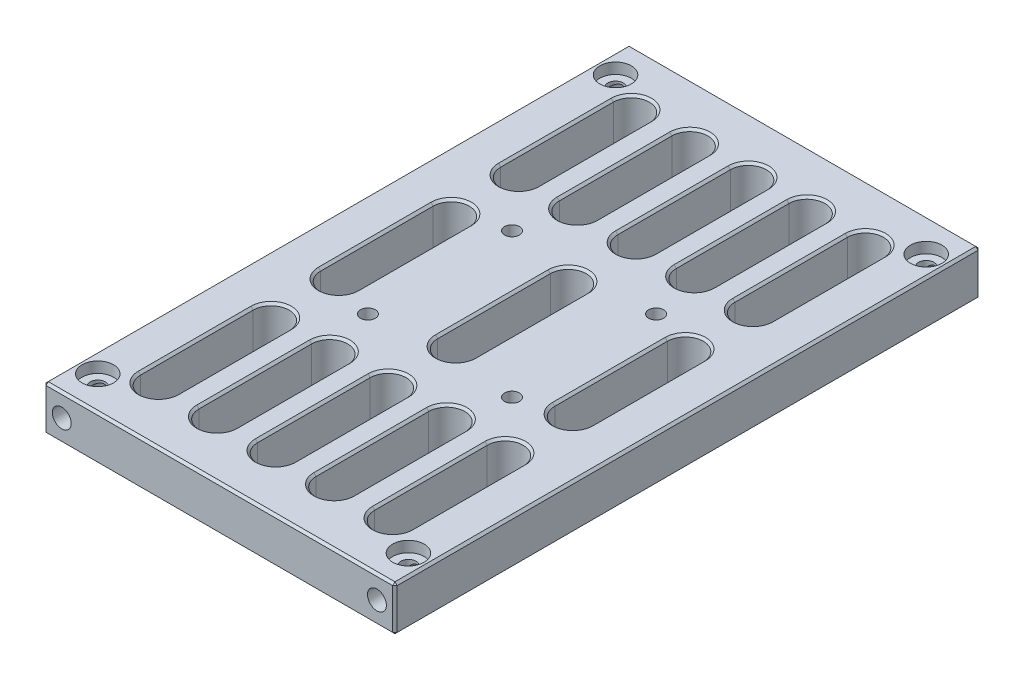
SolidWorks part; units mm, degrees
ref_plane "Plan de face" through (0, 0, 0) normal (0, 0, 1) x (1, 0, 0)
ref_plane "Plan de dessus" through (0, 0, 0) normal (0, 1, 0) x (1, 0, 0)
ref_plane "Plan de droite" through (0, 0, 0) normal (1, 0, 0) x (0, 0, -1)
sketch "Esquisse1" plane through (0, 0, 0) normal (0, 0, 1) x (1, 0, 0)
  line L1 (-39, 0.2172) -> (39, 0.2172)
  line L2 (-39, 0.2172) -> (-39, -9.7828)
  line L3 (-39, -9.7828) -> (39, -9.7828)
  line L4 (39, 0.2172) -> (39, -9.7828)
extrude "Boss.-Extru.1" add sketch "Esquisse1" along normal blind 130
sketch "Esquisse2" plane through (0, 0, 130) normal (0, 0, 1) x (1, 0, 0)
  line L0 (-52.4107, -4.7828) -> (51.3292, -4.7828) construction
  line L1 (39, 0.2172) -> (-39, 0.2172) construction
  line L2 (-35, 10.8156) -> (-35, -20.714) construction
  line L3 (35, 10.8156) -> (35, -20.714) construction
hole_wizard "Trou taraudé M5x0.81" positions "Esquisse3D1" profile "Esquisse3" tap size "M5x0.8" standard "Ansi Metric"
sketch3d "Esquisse3D1"
  line L0 (-52.4107, -4.7828, 130) -> (51.3292, -4.7828, 130) construction
  line L1 (-35, 10.8156, 130) -> (-35, -20.714, 130) construction
  line L2 (35, 10.8156, 130) -> (35, -20.714, 130) construction
  point P0 (-35, -4.7828, 130)
  point P6 (35, -4.7828, 130)
cosmetic thread "Filetage de perçage1" parameters "D1"=25, "D2"=5
cosmetic thread "Filetage de perçage2" parameters "D1"=25, "D2"=5
sketch "Esquisse3" plane through (-35, -4.7828, 130) normal (1, 0, 0) x (0, -1, 0)
  line L0 (0, 0) -> (0, 26.2618)
  line L1 (0, 26.2618) -> (2.1, 25)
  line L2 (2.1, 25) -> (2.1, 0)
  line L5 (2.1, 0) -> (0, 0)
  line L10 (0, 26.2618) -> (-2.1, 25) construction
  line L11 (0, -6.35) -> (0, 107.95) construction
  dimension "Diamètre du trou pour taraudage" = 4.2
  dimension "Profondeur du trou pour taraudage" = 25
  dimension "Angle de pointe" = 118
hole_wizard "Trou taraudé M5x0.82" positions "Esquisse4" profile "Esquisse5" tap size "M5x0.8" standard "Ansi Metric"
sketch "Esquisse4" plane through (0, 0, 0) normal (0, 0, -1) x (-1, 0, 0)
  line L0 (200052.4107, -4.7828) -> (-200051.3292, -4.7828) construction
  line L1 (-35, 10.8156) -> (-35, -20.714) construction
  line L2 (35, 10.8156) -> (35, -20.714) construction
  point P0 (-35, -4.7828)
  point P6 (35, -4.7828)
sketch "Esquisse5" plane through (35, -4.7828, 0) normal (1, 0, 0) x (0, 1, 0)
  line L0 (0, 0) -> (0, 29.4618)
  line L1 (0, 29.4618) -> (2.1, 28.2)
  line L2 (2.1, 28.2) -> (2.1, 0)
  line L5 (2.1, 0) -> (0, 0)
  line L10 (0, 29.4618) -> (-2.1, 28.2) construction
  line L11 (0, -6.35) -> (0, 107.95) construction
  dimension "Diamètre du trou pour taraudage" = 4.2
  dimension "Profondeur du trou pour taraudage" = 28.2
  dimension "Angle de pointe" = 118
cosmetic thread "Filetage de perçage3" parameters "D1"=24.2, "D2"=5
cosmetic thread "Filetage de perçage4" parameters "D1"=24.2, "D2"=5
sketch "Esquisse6" plane through (0, 0.2172, 0) normal (0, 1, 0) x (1, 0, 0)
  line L0 (0, 12.0068) -> (0, -135.3984) construction
  line L1 (54.4844, -65) -> (-55.2769, -65) construction
  line L2 (54.4844, -49) -> (-55.2769, -49) construction
  line L3 (16, -91.2165) -> (16, -33.1658) construction
  line L4 (54.4844, -81) -> (-55.2769, -81) construction
  line L5 (-16, -91.2165) -> (-16, -33.1658) construction
  dimension "D1" = 16
  dimension "D2" = 16
  dimension "D3" = 16
  dimension "D4" = 16
hole_wizard "Trou taraudé M4x0.71" positions "Esquisse3D2" profile "Esquisse7" tap size "M4x0.7" standard "Ansi Metric" end condition up to next
sketch3d "Esquisse3D2"
  line L0 (16, 0.2172, 91.2165) -> (16, 0.2172, 33.1658) construction
  line L1 (54.4844, 0.2172, 81) -> (-55.2769, 0.2172, 81) construction
  line L2 (54.4844, 0.2172, 49) -> (-55.2769, 0.2172, 49) construction
  line L3 (-16, 0.2172, 91.2165) -> (-16, 0.2172, 33.1658) construction
  point P0 (16, 0.2172, 81)
  point P6 (16, 0.2172, 49)
  point P10 (-16, 0.2172, 49)
  point P14 (-16, 0.2172, 81)
sketch "Esquisse7" plane through (16, 0.2172, 81) normal (1, 0, 0) x (0, 0, 1)
  line L0 (0, 0) -> (0, 10)
  line L1 (0, 10) -> (1.65, 10)
  line L2 (1.65, 10) -> (1.65, 0)
  line L5 (1.65, 0) -> (0, 0)
  line L11 (0, -6.35) -> (0, 107.95) construction
  dimension "Diamètre du trou pour taraudage jusqu'au prochain" = 3.3
  dimension "Profondeur du trou pour taraudage jusqu'au prochain" = 10
cosmetic thread "Filetage de perçage5" parameters "D2"=4
cosmetic thread "Filetage de perçage6" parameters "D2"=4
cosmetic thread "Filetage de perçage7" parameters "D2"=4
cosmetic thread "Filetage de perçage8" parameters "D2"=4
sketch "Esquisse8" plane through (0, 0.2172, 0) normal (0, 1, 0) x (1, 0, 0)
  line L0 (-34.5, 44.3525) -> (-34.5, -155.5225) construction
  line L1 (34.5, 44.3525) -> (34.5, -155.5225) construction
  line L2 (-62.6243, -7.5) -> (73.6594, -7.5) construction
  line L3 (39, 0) -> (-39, 0) construction
  line L4 (-62.6243, -122.5) -> (73.6594, -122.5) construction
  line L5 (39, -130) -> (-39, -130) construction
  dimension "D1" = 34.5
  dimension "D2" = 69
  dimension "D3" = 7.5
  dimension "D4" = 7.5
hole_wizard "Chambrage pour vis à tête ronde bombée M31" positions "Esquisse9" profile "Esquisse10" counterbore size "M3" standard "Ansi Metric" end condition through all
sketch "Esquisse9" plane through (0, 0.2172, 0) normal (0, 1, 0) x (1, 0, 0)
  line L0 (-34.5, 44.3525) -> (-34.5, -155.5225) construction
  line L1 (-62.6243, -7.5) -> (73.6594, -7.5) construction
  line L2 (34.5, 44.3525) -> (34.5, -155.5225) construction
  line L3 (-62.6243, -122.5) -> (73.6594, -122.5) construction
  point P0 (-34.5, -7.5)
  point P6 (34.5, -7.5)
  point P10 (34.5, -122.5)
  point P14 (-34.5, -122.5)
sketch "Esquisse10" plane through (-34.5, 0.2172, 7.5) normal (1, 0, 0) x (0, 0, 1)
  line L0 (0, 0) -> (0, 10)
  line L1 (0, 10) -> (1.7, 10)
  line L3 (1.7, 10) -> (1.7, 2.4)
  line L4 (1.7, 2.4) -> (3.5, 2.4)
  line L5 (3.5, 2.4) -> (3.5, 0)
  line L7 (3.5, 0) -> (0, 0)
  line L11 (0, -6.35) -> (0, 107.95) construction
  dimension "Diamètre du perçage jusqu'au prochain" = 3.4
  dimension "Profondeur du perçage jusqu'au prochain" = 10
  dimension "Diamètre du chambrage" = 7
  dimension "Profondeur du chambrage" = 2.4
sketch "Esquisse11" plane through (0, -9.7828, 0) normal (0, -1, 0) x (-1, 0, 0)
  line L0 (-26, -138.9018) -> (-26, 17.221) construction
  line L3 (0, -138.9018) -> (0, 17.221) construction
  line L4 (26, -138.9018) -> (26, 17.221) construction
  line L5 (-13, -138.9018) -> (-13, 17.221) construction
  line L6 (13, -138.9018) -> (13, 17.221) construction
  line L7 (-48.4591, -105) -> (51.9254, -105) construction
  line L8 (-48.4591, -65) -> (51.9254, -65) construction
  line L9 (-48.4591, -25) -> (51.9254, -25) construction
  line L10 (39, -130) -> (-39, -130) construction
  line L11 (39, 0) -> (-39, 0) construction
  line L12 (-39, -130) -> (-39, 0) construction
  line L13 (39, -130) -> (39, 0) construction
  line L14 (-26, -117.5) -> (-26, -92.5) construction
  line L15 (-30, -117.5) -> (-30, -92.5)
  line L16 (-22, -117.5) -> (-22, -92.5)
  line L17 (-13, -117.5) -> (-13, -92.5) construction
  line L18 (-17, -117.5) -> (-17, -92.5)
  line L19 (-9, -117.5) -> (-9, -92.5)
  line L20 (0, -117.5) -> (0, -92.5) construction
  line L23 (-4, -117.5) -> (-4, -92.5)
  line L24 (4, -117.5) -> (4, -92.5)
  line L25 (13, -117.5) -> (13, -92.5) construction
  line L26 (9, -117.5) -> (9, -92.5)
  line L27 (17, -117.5) -> (17, -92.5)
  line L28 (26, -117.5) -> (26, -92.5) construction
  line L29 (22, -117.5) -> (22, -92.5)
  line L30 (30, -117.5) -> (30, -92.5)
  line L31 (-26, -77.5) -> (-26, -52.5) construction
  line L32 (-30, -77.5) -> (-30, -52.5)
  line L33 (-22, -77.5) -> (-22, -52.5)
  line L34 (0, -77.5) -> (0, -52.5) construction
  line L35 (-4, -77.5) -> (-4, -52.5)
  line L36 (4, -77.5) -> (4, -52.5)
  line L37 (26, -77.5) -> (26, -52.5) construction
  line L38 (22, -77.5) -> (22, -52.5)
  line L39 (30, -77.5) -> (30, -52.5)
  line L40 (-26, -37.5) -> (-26, -12.5) construction
  line L41 (-30, -37.5) -> (-30, -12.5)
  line L42 (-22, -37.5) -> (-22, -12.5)
  line L43 (-13, -37.5) -> (-13, -12.5) construction
  line L44 (-17, -37.5) -> (-17, -12.5)
  line L45 (-9, -37.5) -> (-9, -12.5)
  line L46 (0, -37.5) -> (0, -12.5) construction
  line L47 (-4, -37.5) -> (-4, -12.5)
  line L48 (4, -37.5) -> (4, -12.5)
  line L49 (13, -37.5) -> (13, -12.5) construction
  line L50 (9, -37.5) -> (9, -12.5)
  line L51 (17, -37.5) -> (17, -12.5)
  line L52 (26, -37.5) -> (26, -12.5) construction
  line L53 (22, -37.5) -> (22, -12.5)
  line L54 (30, -37.5) -> (30, -12.5)
  arc A2 (-30, -117.5) -> (-22, -117.5) centre (-26, -117.5) ccw
  arc A3 (-22, -92.5) -> (-30, -92.5) centre (-26, -92.5) ccw
  arc A4 (-17, -117.5) -> (-9, -117.5) centre (-13, -117.5) ccw
  arc A5 (-9, -92.5) -> (-17, -92.5) centre (-13, -92.5) ccw
  arc A8 (-4, -117.5) -> (4, -117.5) centre (0, -117.5) ccw
  arc A9 (4, -92.5) -> (-4, -92.5) centre (0, -92.5) ccw
  arc A10 (9, -117.5) -> (17, -117.5) centre (13, -117.5) ccw
  arc A11 (17, -92.5) -> (9, -92.5) centre (13, -92.5) ccw
  arc A12 (22, -117.5) -> (30, -117.5) centre (26, -117.5) ccw
  arc A13 (30, -92.5) -> (22, -92.5) centre (26, -92.5) ccw
  arc A14 (-30, -77.5) -> (-22, -77.5) centre (-26, -77.5) ccw
  arc A15 (-22, -52.5) -> (-30, -52.5) centre (-26, -52.5) ccw
  arc A16 (-4, -77.5) -> (4, -77.5) centre (0, -77.5) ccw
  arc A17 (4, -52.5) -> (-4, -52.5) centre (0, -52.5) ccw
  arc A18 (22, -77.5) -> (30, -77.5) centre (26, -77.5) ccw
  arc A19 (30, -52.5) -> (22, -52.5) centre (26, -52.5) ccw
  arc A20 (-30, -37.5) -> (-22, -37.5) centre (-26, -37.5) ccw
  arc A21 (-22, -12.5) -> (-30, -12.5) centre (-26, -12.5) ccw
  arc A22 (-17, -37.5) -> (-9, -37.5) centre (-13, -37.5) ccw
  arc A23 (-9, -12.5) -> (-17, -12.5) centre (-13, -12.5) ccw
  arc A24 (-4, -37.5) -> (4, -37.5) centre (0, -37.5) ccw
  arc A25 (4, -12.5) -> (-4, -12.5) centre (0, -12.5) ccw
  arc A26 (9, -37.5) -> (17, -37.5) centre (13, -37.5) ccw
  arc A27 (17, -12.5) -> (9, -12.5) centre (13, -12.5) ccw
  arc A28 (22, -37.5) -> (30, -37.5) centre (26, -37.5) ccw
  arc A29 (30, -12.5) -> (22, -12.5) centre (26, -12.5) ccw
  point P27 (-26, -105)
  point P33 (-13, -105)
  point P41 (0, -105)
  point P47 (13, -105)
  point P55 (26, -105)
  point P61 (-26, -65)
  point P68 (0, -65)
  point P75 (26, -65)
  point P82 (-26, -25)
  point P89 (-13, -25)
  point P96 (0, -25)
  point P103 (13, -25)
  point P110 (26, -25)
  dimension "D1" = 25
  dimension "D2" = 25
  dimension "D3" = 65
  dimension "D4" = 13
  dimension "D5" = 26
  dimension "D6" = 13
  dimension "D7" = 26
extrude "Enlèv. mat.-Extru.1" cut sketch "Esquisse11" against normal through all
chamfer "Chanfrein1" distance 0.5 angle 45 12 edges at (-39, -4.7828, 0) (-39, 0.2172, 65) (-39, -9.7828, 65) (-39, -4.7828, 130) (0, 0.2172, 130) (0, -9.7828, 130) (39, -4.7828, 130) (39, 0.2172, 65) (0, 0.2172, 0) (39, -4.7828, 0) (0, -9.7828, 0) (39, -9.7828, 65)
chamfer "Chanfrein2" distance 0.5 angle 45 104 edges at (26, 0.2172, 41.5) (30, 0.2172, 25) (26, 0.2172, 8.5) (22, 0.2172, 25) (13, 0.2172, 41.5) (17, 0.2172, 25) (13, 0.2172, 8.5) (9, 0.2172, 25) (0, 0.2172, 41.5) (4, 0.2172, 25) (0, 0.2172, 8.5) (-4, 0.2172, 25) (-13, 0.2172, 41.5) (-9, 0.2172, 25) (-13, 0.2172, 8.5) (-17, 0.2172, 25) (-26, 0.2172, 41.5) (-22, 0.2172, 25) (-26, 0.2172, 8.5) (-30, 0.2172, 25) (-26, 0.2172, 81.5) (-30, 0.2172, 65) (-26, 0.2172, 48.5) (-22, 0.2172, 65) (0, 0.2172, 81.5) (-4, 0.2172, 65) (0, 0.2172, 48.5) (4, 0.2172, 65) (26, 0.2172, 81.5) (22, 0.2172, 65) (26, 0.2172, 48.5) (30, 0.2172, 65) (26, 0.2172, 121.5) (30, 0.2172, 105) (26, 0.2172, 88.5) (22, 0.2172, 105) (13, 0.2172, 121.5) (17, 0.2172, 105) (13, 0.2172, 88.5) (9, 0.2172, 105) (0, 0.2172, 121.5) (4, 0.2172, 105) (0, 0.2172, 88.5) (-4, 0.2172, 105) (-13, 0.2172, 121.5) (-9, 0.2172, 105) (-13, 0.2172, 88.5) (-17, 0.2172, 105) (-26, 0.2172, 121.5) (-22, 0.2172, 105) (-26, 0.2172, 88.5) (-30, 0.2172, 105) (-26, -9.7828, 8.5) (-30, -9.7828, 25) (-26, -9.7828, 41.5) (-22, -9.7828, 25) (-13, -9.7828, 41.5) (-17, -9.7828, 25) (-13, -9.7828, 8.5) (-9, -9.7828, 25) (0, -9.7828, 8.5) (-4, -9.7828, 25) (0, -9.7828, 41.5) (4, -9.7828, 25) (13, -9.7828, 41.5) (9, -9.7828, 25) (13, -9.7828, 8.5) (17, -9.7828, 25) (26, -9.7828, 8.5) (22, -9.7828, 25) (26, -9.7828, 41.5) (30, -9.7828, 25) (26, -9.7828, 81.5) (30, -9.7828, 65) (26, -9.7828, 48.5) (22, -9.7828, 65) (0, -9.7828, 81.5) (4, -9.7828, 65) (-4, -9.7828, 65) (0, -9.7828, 48.5) (-26, -9.7828, 81.5) (-30, -9.7828, 65) (-26, -9.7828, 48.5) (-22, -9.7828, 65) (26, -9.7828, 121.5) (30, -9.7828, 105) (26, -9.7828, 88.5) (22, -9.7828, 105) (13, -9.7828, 88.5) (17, -9.7828, 105) (13, -9.7828, 121.5) (9, -9.7828, 105) (0, -9.7828, 121.5) (4, -9.7828, 105) (0, -9.7828, 88.5) (-4, -9.7828, 105) (-26, -9.7828, 88.5) (-30, -9.7828, 105) (-26, -9.7828, 121.5) (-22, -9.7828, 105) (-13, -9.7828, 121.5) (-17, -9.7828, 105) (-13, -9.7828, 88.5) (-9, -9.7828, 105)
equation "\"D3@Esquisse1\"= \"D1@Esquisse1\" * 2"
equation "\"D3@Esquisse2\"= \"D2@Esquisse2\""
